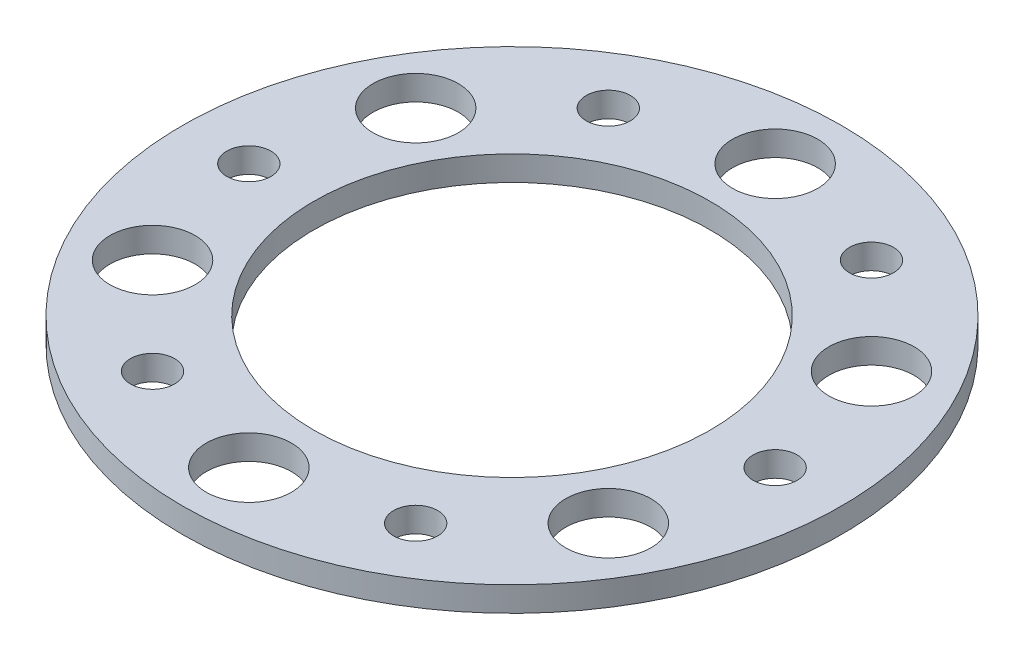
SolidWorks part; units mm, degrees
material "Stainless Steel (ferritic)"
ref_plane "Front Plane" through (0, 0, 0) normal (0, 0, 1) x (1, 0, 0)
ref_plane "Top Plane" through (0, 0, 0) normal (0, 1, 0) x (1, 0, 0)
ref_plane "Right Plane" through (0, 0, 0) normal (1, 0, 0) x (0, 0, -1)
sketch "Sketch1" plane through (0, 0, 0) normal (0, 1, 0) x (1, 0, 0)
  circle A0 centre (0, 0) radius 16.891
  circle A1 centre (0, 0) radius 10.16
  dimension "D1" = 33.782
  dimension "D2" = 20.32
extrude "Boss-Extrude1" add sketch "Sketch1" along normal blind 1.27
sketch "Sketch2" plane through (0, 1.27, 0) normal (0, 1, 0) x (1, 0, 0)
  line L0 (0, 0) -> (0, 24.9997) construction
  circle A0 centre (0, 13.4874) radius 2.1844
  circle A1 centre (-11.6804, 6.7437) radius 2.1844
  circle A2 centre (-11.6804, -6.7437) radius 2.1844
  circle A3 centre (0, -13.4874) radius 2.1844
  circle A4 centre (11.6804, -6.7437) radius 2.1844
  circle A5 centre (11.6804, 6.7437) radius 2.1844
  point P17 (0, 0)
  dimension "D2" = 4.3688
  dimension "D1" = 13.4874
  dimension "D3" = 6
extrude "Cut-Extrude1" cut sketch "Sketch2" against normal through all
hole_wizard "#4-40 Tapped Hole1" positions "Sketch7" profile "Sketch6" tap size "#4-40" standard "ANSI Inch" end condition through all
sketch "Sketch7" plane through (0, 1.27, 0) normal (0, 1, 0) x (1, 0, 0)
  line L0 (0, 0) -> (0, 13.4874) construction
  line L2 (0, 0) -> (-11.3544, 19.6664) construction
  point P12 (-6.7437, 11.6804)
  point P19 (6.7437, 11.6804)
  point P20 (13.4874, 0)
  point P21 (6.7437, -11.6804)
  point P22 (-6.7437, -11.6804)
  point P23 (-13.4874, 0)
  point P24 (0, 0)
  dimension "D1" = 30
  dimension "D2" = 13.4874
  dimension "D3" = 6
sketch "Sketch6" plane through (0, 1.27, 0) normal (1, 0, 0) x (0, 0, 1)
  line L0 (0, 0) -> (0, 1.27)
  line L1 (0, 1.27) -> (1.1303, 1.27)
  line L2 (1.1303, 1.27) -> (1.1303, 0)
  line L5 (1.1303, 0) -> (0, 0)
  line L11 (0, -6.35) -> (0, 107.95) construction
  dimension "Thru Tap Drill Dia." = 2.2606
  dimension "Thru Tap Drill Depth" = 1.27
cosmetic thread "Hole Thread9" parameters "D2"=2.8448
cosmetic thread "Hole Thread10" parameters "D2"=2.8448
cosmetic thread "Hole Thread11" parameters "D2"=2.8448
cosmetic thread "Hole Thread12" parameters "D2"=2.8448
cosmetic thread "Hole Thread13" parameters "D2"=2.8448
cosmetic thread "Hole Thread14" parameters "D2"=2.8448
